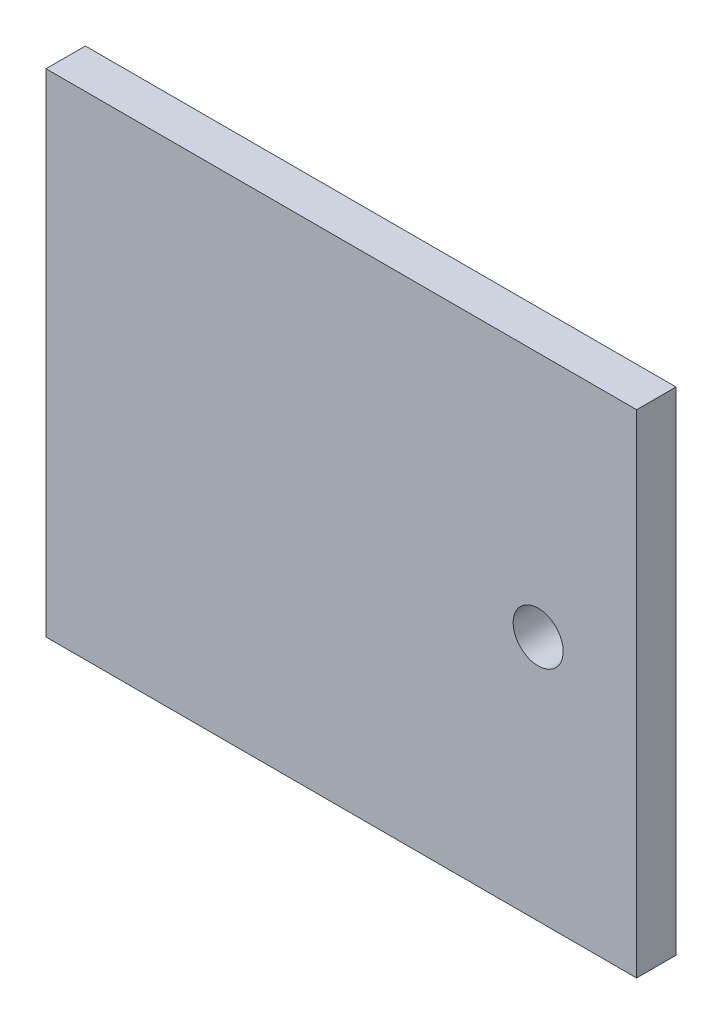
SolidWorks part; units mm, degrees
ref_plane "Front Plane" through (0, 0, 0) normal (0, 0, 1) x (1, 0, 0)
ref_plane "Top Plane" through (0, 0, 0) normal (0, 1, 0) x (1, 0, 0)
ref_plane "Right Plane" through (0, 0, 0) normal (1, 0, 0) x (0, 0, -1)
sketch "Sketch1" plane through (0, 0, 0) normal (0, 0, 1) x (1, 0, 0)
  line L1 (-150, -125) -> (150, -125)
  line L2 (-150, -125) -> (-150, 125)
  line L3 (-150, 125) -> (150, 125)
  line L4 (150, -125) -> (150, 125)
  line L5 (-150, -125) -> (150, 125) construction
  line L6 (-150, 125) -> (150, -125) construction
  point P0 (0, 0)
  dimension "D1" = 250
  dimension "D2" = 300
extrude "Boss-Extrude1" add sketch "Sketch1" along normal blind 20
sketch "Sketch2" plane through (0, 0, 20) normal (0, 0, 1) x (1, 0, 0)
  line L0 (150, -125) -> (150, 125) construction
  circle A0 centre (100, 0) radius 12.7
  dimension "D1" = 25.4
  dimension "D2" = 50
extrude "Cut-Extrude1" cut sketch "Sketch2" against normal blind 20
